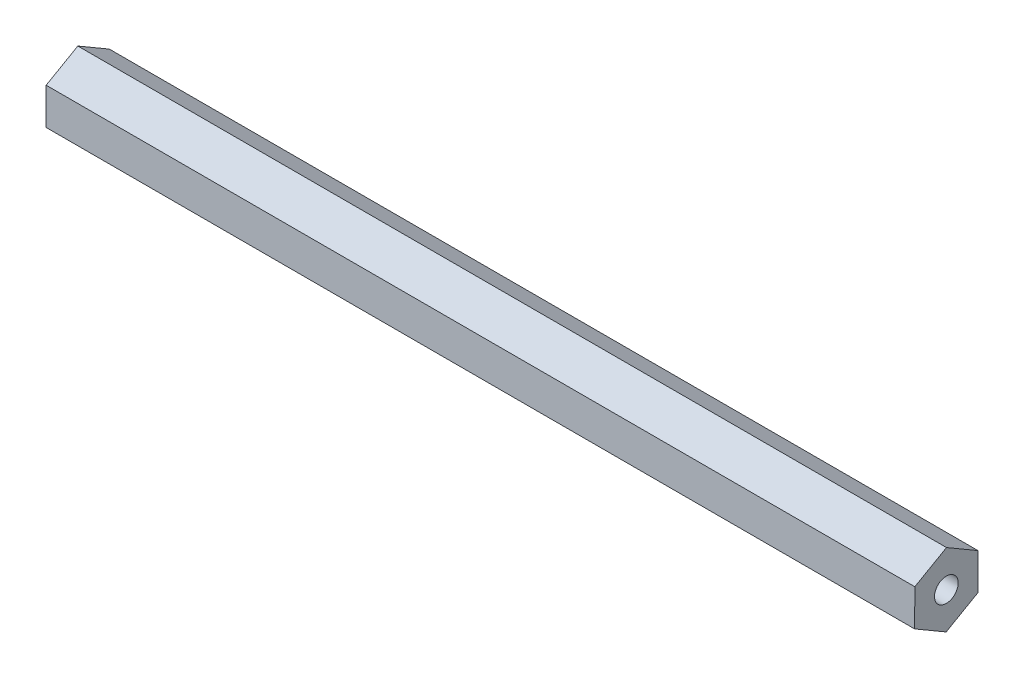
SolidWorks part; units mm, degrees
ref_plane "Front Plane" through (0, 0, 0) normal (0, 0, 1) x (1, 0, 0)
ref_plane "Top Plane" through (0, 0, 0) normal (0, 1, 0) x (1, 0, 0)
ref_plane "Right Plane" through (0, 0, 0) normal (1, 0, 0) x (0, 0, -1)
sketch "Sketch1" plane through (0, 0, 0) normal (1, 0, 0) x (0, 0, -1)
  line L1 (6.3663, 3.6379) -> (0.0326, 7.3323)
  line L2 (0.0326, 7.3323) -> (-6.3336, 3.6944)
  line L3 (-6.3336, 3.6944) -> (-6.3663, -3.6379)
  line L4 (-6.3663, -3.6379) -> (-0.0326, -7.3323)
  line L5 (-0.0326, -7.3323) -> (6.3336, -3.6944)
  line L6 (6.3336, -3.6944) -> (6.3663, 3.6379)
  circle A0 centre (0, 0) radius 6.35 construction
  circle A1 centre (0, 0) radius 2.3813
  dimension "D2" = 4.7625
  dimension "D1" = 12.7
extrude "Boss-Extrude1" add sketch "Sketch1" along normal blind 174.625 contours L1 L2 L3 L4 L5 L6 | A1
